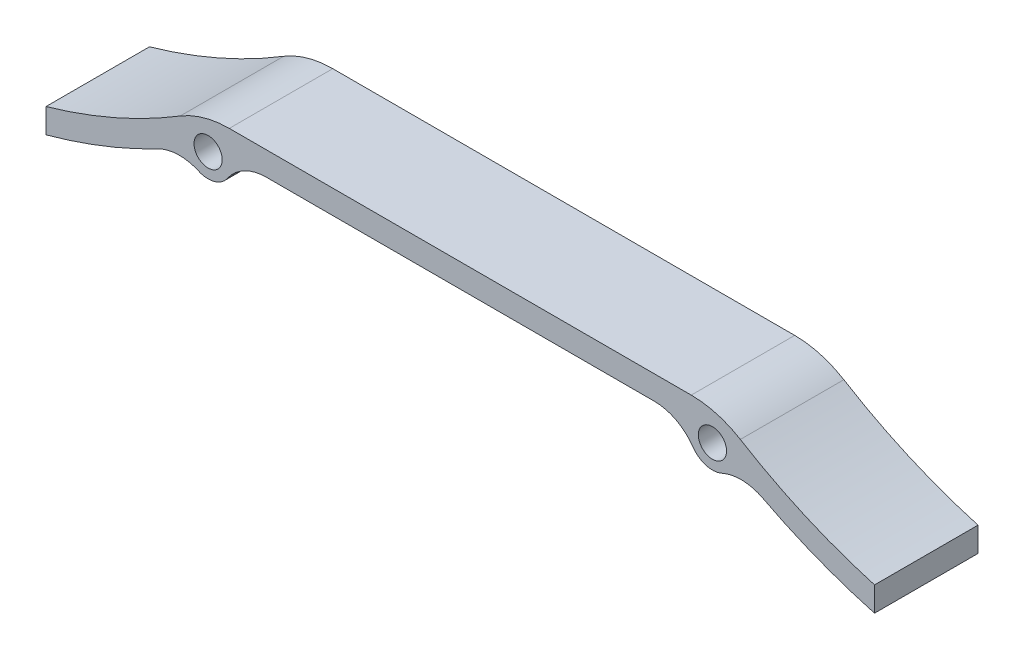
SolidWorks part; units mm, degrees
ref_plane "Plano frontal" through (0, 0, 0) normal (0, 0, 1) x (1, 0, 0)
ref_plane "Plano superior" through (0, 0, 0) normal (0, 1, 0) x (1, 0, 0)
ref_plane "Plano direito" through (0, 0, 0) normal (1, 0, 0) x (0, 0, -1)
sketch "Esboço1" plane through (0, 0, 0) normal (0, 0, 1) x (1, 0, 0)
  line L0 (-49.1191, 68) -> (49.1191, 68)
  line L7 (-88.0945, 47.3219) -> (-88.0945, 52.54)
  line L39 (-41.2651, 62.9464) -> (41.2651, 62.9464)
  line L48 (88.0945, 47.3219) -> (88.0945, 52.54)
  arc A0 (-49.5046, 58.613) -> (-55.6588, 56.879) centre (-53.6243, 61.4464) cw
  arc A1 (88.0945, 52.54) -> (59.5611, 65.0577) centre (119.6025, 163.1395) cw
  arc A9 (-49.5046, 58.613) -> (-41.2651, 62.9464) centre (-41.2651, 52.9464) cw
  arc A13 (-64.3407, 56.6167) -> (-55.6588, 56.879) centre (-59.7277, 47.7442) cw
  arc A15 (59.5611, 65.0577) -> (49.1191, 68) centre (49.1191, 48) ccw
  arc A17 (-88.0945, 47.3219) -> (-64.3407, 56.6167) centre (-119.697, 163.0858) ccw
  circle A19 centre (-53.6243, 61.4464) radius 3
  arc A23 (-59.5611, 65.0577) -> (-49.1191, 68) centre (-49.1191, 48) cw
  arc A25 (88.0945, 47.3219) -> (64.3407, 56.6167) centre (119.697, 163.0858) cw
  arc A27 (64.3407, 56.6167) -> (55.6588, 56.879) centre (59.7277, 47.7442) ccw
  arc A29 (49.5046, 58.613) -> (41.2651, 62.9464) centre (41.2651, 52.9464) ccw
  circle A39 centre (53.6243, 61.4464) radius 3
  arc A44 (-88.0945, 52.54) -> (-59.5611, 65.0577) centre (-119.6025, 163.1395) ccw
  arc A46 (49.5046, 58.613) -> (55.6588, 56.879) centre (53.6243, 61.4464) ccw
  point P1 (-45.9198, 61.797)
extrude "Ressalto-extrusão1" add sketch "Esboço1" along normal blind 22
